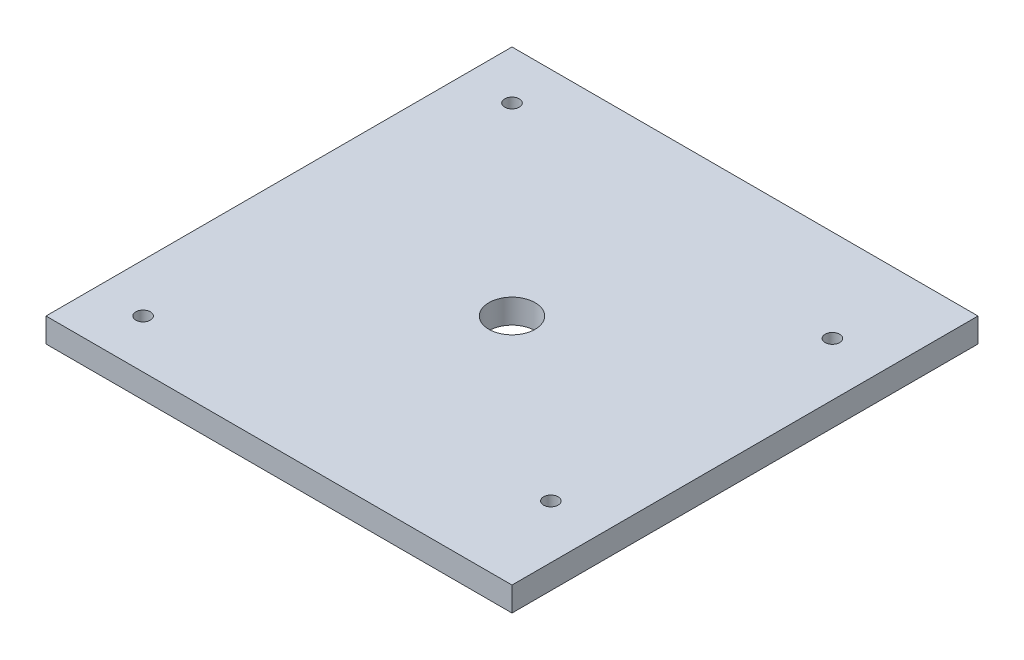
SolidWorks part; units mm, degrees
material "1060 Alloy"
ref_plane "Front Plane" through (0, 0, 0) normal (0, 0, 1) x (1, 0, 0)
ref_plane "Top Plane" through (0, 0, 0) normal (0, 1, 0) x (1, 0, 0)
ref_plane "Right Plane" through (0, 0, 0) normal (1, 0, 0) x (0, 0, -1)
sketch "Sketch1" plane through (0, 0, 0) normal (0, 1, 0) x (1, 0, 0)
  line L0 (0, 48) -> (96, 48) construction
  line L1 (0, 0) -> (96, 0)
  line L2 (0, 0) -> (0, 96)
  line L3 (0, 96) -> (96, 96)
  line L4 (96, 0) -> (96, 96)
  circle A1 centre (10, 10) radius 1.5
  circle A2 centre (85, 19) radius 1.5
  circle A4 centre (85, 77) radius 1.5
  circle A5 centre (10, 86) radius 1.5
  dimension "D5" = 58
  dimension "D6" = 76
  dimension "D4" = 3
  dimension "D3" = 3
  dimension "D1" = 96
  dimension "D2" = 96
  dimension "D7" = 75
  dimension "D8" = 10
extrude "Boss-Extrude1" add sketch "Sketch1" along normal blind 5
sketch "Sketch2" plane through (0, 5, 0) normal (0, 1, 0) x (1, 0, 0)
  line L0 (48, 96) -> (48, 0) construction
  line L1 (96, 96) -> (0, 96) construction
  line L2 (0, 0) -> (96, 0) construction
  circle A0 centre (48, 48) radius 4.7625
  dimension "D1" = 9.525
extrude "Cut-Extrude1" cut sketch "Sketch2" against normal through all
